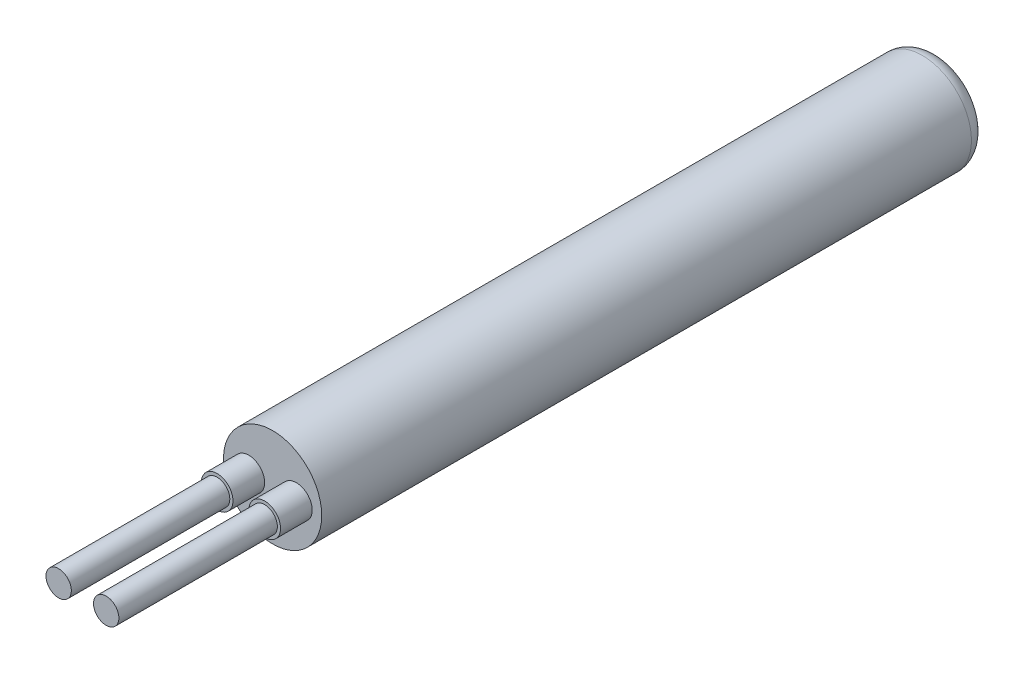
SolidWorks part; units mm, degrees
ref_plane "Alzado" through (0, 0, 0) normal (0, 0, 1) x (1, 0, 0)
ref_plane "Planta" through (0, 0, 0) normal (0, 1, 0) x (1, 0, 0)
ref_plane "Vista lateral" through (0, 0, 0) normal (1, 0, 0) x (0, 0, -1)
sketch "Croquis1" plane through (0, 0, 0) normal (0, 0, 1) x (1, 0, 0)
  circle A0 centre (0, 0) radius 1.55
  dimension "D1" = 3.1
extrude "Saliente-Extruir1" add sketch "Croquis1" along normal blind 21
sketch "Croquis2" plane through (0, 0, 21) normal (0, 0, 1) x (1, 0, 0)
  circle A0 centre (0.75, 0) radius 0.4
  circle A1 centre (-0.75, 0) radius 0.4
  dimension "D1" = 0.8
  dimension "D2" = 1.5
  dimension "D3" = 0.75
extrude "Saliente-Extruir2" add sketch "Croquis2" along normal blind 6
sketch "Croquis3" plane through (0, 0, 21) normal (0, 0, 1) x (1, 0, 0)
  circle A0 centre (-0.75, 0) radius 0.5
  circle A1 centre (0.75, 0) radius 0.5
  circle A2 centre (0.75, 0) radius 0.4 construction
  circle A3 centre (-0.75, 0) radius 0.4 construction
  circle A4 centre (0.75, 0) radius 0.4
  circle A5 centre (-0.75, 0) radius 0.4
  dimension "D1" = 1
  dimension "D2" = 1
extrude "Saliente-Extruir3" add sketch "Croquis3" along normal blind 1
fillet "Redondeo1" radius 0.5 1 edges at (1.55, 0, 0)
